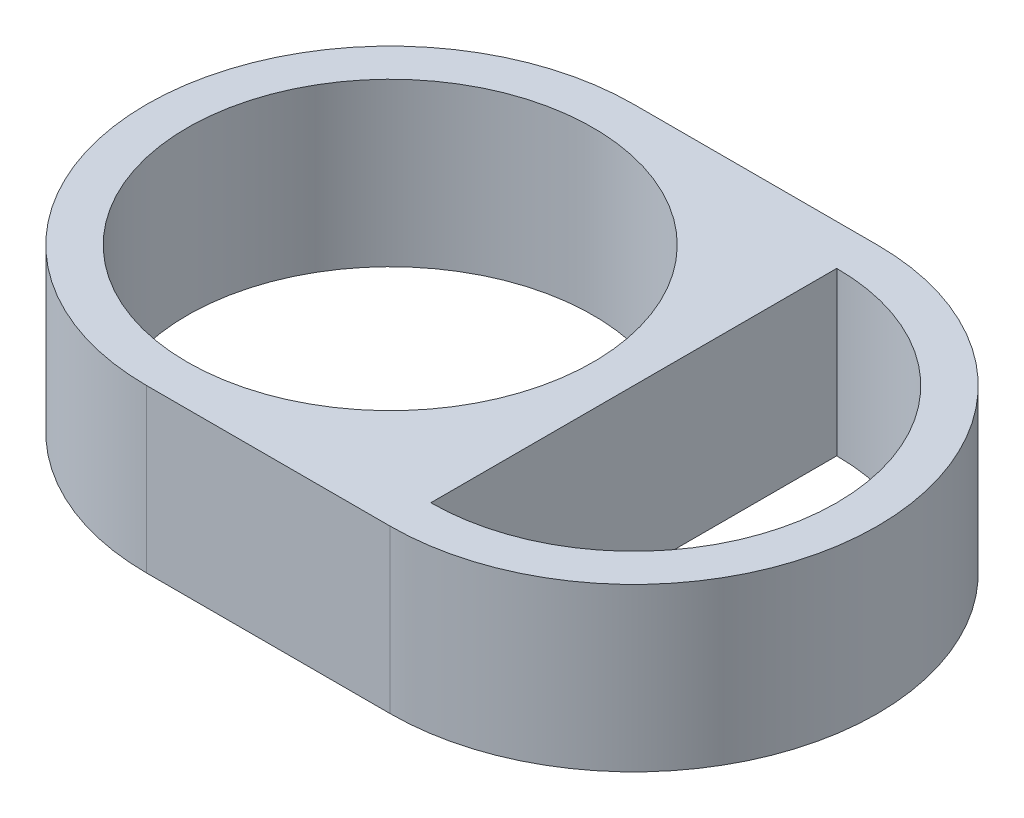
SolidWorks part; units mm, degrees
material "1060 合金"
ref_plane "前视基准面" through (0, 0, 0) normal (0, 0, 1) x (1, 0, 0)
ref_plane "上视基准面" through (0, 0, 0) normal (0, 1, 0) x (1, 0, 0)
ref_plane "右视基准面" through (0, 0, 0) normal (1, 0, 0) x (0, 0, -1)
sketch "草图1" plane through (0, 0, 0) normal (0, 1, 0) x (1, 0, 0)
  line L0 (0, -12) -> (12, -12)
  line L1 (12, 10) -> (12, -10)
  line L3 (12, 12) -> (0, 12)
  circle A0 centre (0, 0) radius 10
  arc A1 (0, 12) -> (0, -12) centre (0, 0) ccw
  arc A2 (12, 12) -> (12, -12) centre (12, 0) cw
  arc A3 (12, 10) -> (12, -10) centre (12, 0) cw
extrude "凸台-拉伸1" add sketch "草图1" along normal blind 8 contours L3 A1 L0 A2 | A0 | L1 A3
ref_plane "基准面1" through (0, 4, 0) normal (0, 1, 0) x (1, 0, 0)
